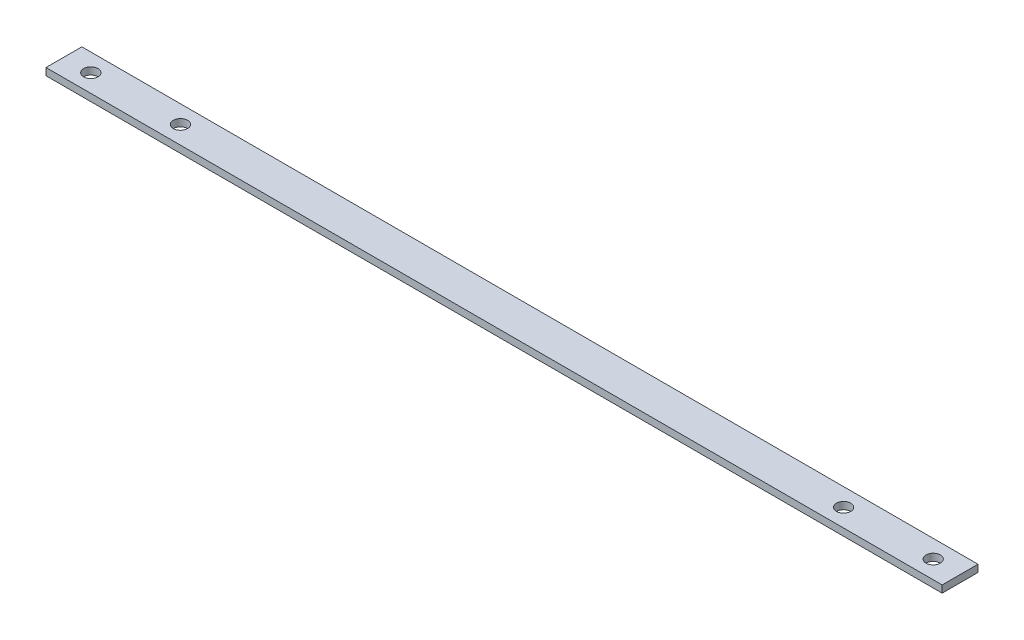
SolidWorks part; units mm, degrees
ref_plane "Спереди" through (0, 0, 0) normal (0, 0, 1) x (1, 0, 0)
ref_plane "Сверху" through (0, 0, 0) normal (0, 1, 0) x (1, 0, 0)
ref_plane "Справа" through (0, 0, 0) normal (1, 0, 0) x (0, 0, -1)
sketch "Эскиз1" plane through (0, 0, 0) normal (1, 0, 0) x (0, 0, -1)
  line L0 (0, 0) -> (20, 0)
extrude "Вытянуть-Тонкостенный1" add sketch "Эскиз1" along normal blind 500 thin
sketch "Эскиз2" plane through (0, 0, 0) normal (0, 1, 0) x (1, 0, 0)
  circle A0 centre (15, 10) radius 4
  circle A1 centre (65, 10) radius 4
  circle A2 centre (435, 10) radius 4
  circle A3 centre (485, 10) radius 4
  dimension "D1" = 2
  dimension "D2" = 2
extrude "Вырез-Вытянуть1" cut sketch "Эскиз2" against normal through all
